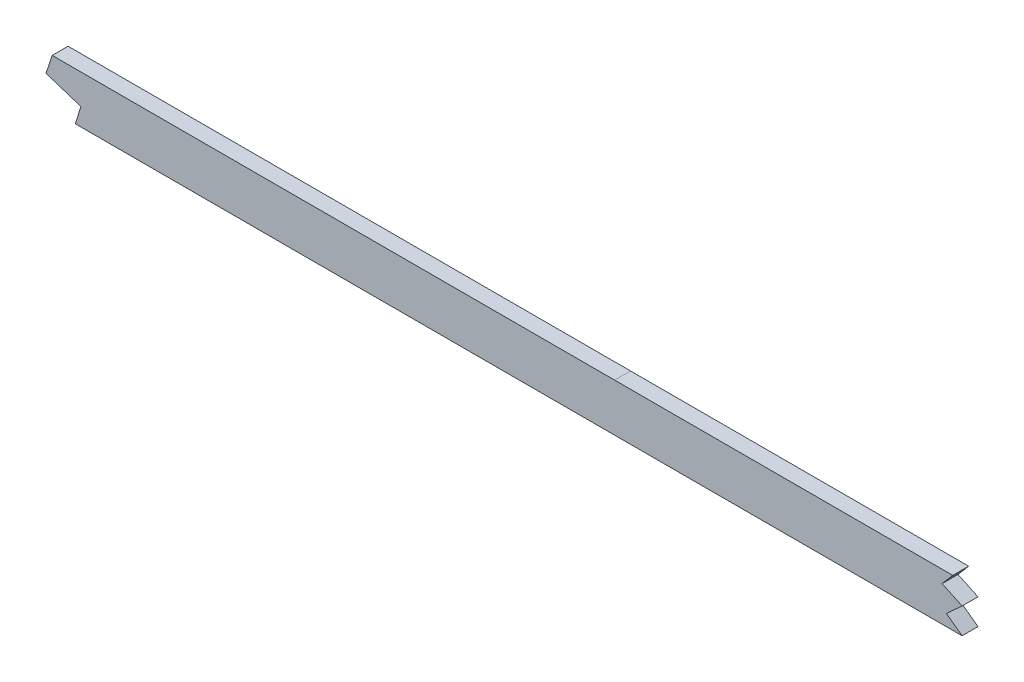
SolidWorks part; units mm, degrees
ref_plane "Front Plane" through (0, 0, 0) normal (0, 0, 1) x (1, 0, 0)
ref_plane "Top Plane" through (0, 0, 0) normal (0, 1, 0) x (1, 0, 0)
ref_plane "Right Plane" through (0, 0, 0) normal (1, 0, 0) x (0, 0, -1)
sketch "Sketch1" plane through (0, 0, 0) normal (0, 0, 1) x (1, 0, 0)
  line L0 (1046.2855, 53.4707) -> (499.61, 53.4707) construction
  line L1 (55, 0) -> (-55, 0) construction
  line L2 (1046.2855, -53.4707) -> (499.61, -53.4707)
  line L3 (1046.2855, -34.4207) -> (499.61, -34.4207)
  line L4 (99.06, -18.1493) -> (99.06, -37.7415)
  line L5 (2669.54, 9.5231) -> (2669.54, -9.569)
  spline S0 degree 5 poles (2699.7923, 7.5245) (2639.6368, 11.6572) (2579.4813, 15.4358) (2518.4981, 19.1485) (2436.3555, 23.2524) (2354.213, 26.6315) (2332.5703, 27.481) (2156.2686, 34.3778) (1979.9669, 41.6286) (1824.1143, 52.7713) (1636.9286, 53.5796) (1449.7429, 53.454) (1418.0067, 53.4707) (1324.8993, 53.4707) (1231.7919, 53.4707) (1170.4413, 53.4707) (1108.7841, 53.4707) (1047.1269, 53.4707) (1046.8464, 53.4707) (1046.5659, 53.4707) (1046.2855, 53.4707) knots 100.654805 100.654805 100.654805 100.654805 100.654805 100.654805 130.927897 130.927897 130.927897 141.337055 141.337055 141.337055 218.101815 218.101815 218.101815 233.772059 233.772059 233.772059 264.077723 264.077723 264.077723 264.216209 264.216209 264.216209 264.216209 264.216209 264.216209 weights 1 1 1 1 1 1 1 1 1 1 1 1 1 1 1 1 1 1 1 1 1 construction
  spline S1 degree 5 poles (499.61, 53.4707) (492.1368, 53.4707) (484.7543, 53.4707) (477.443, 53.4707) (448.5166, 53.4707) (419.5901, 53.4707) (398.3681, 53.4707) (355.6475, 53.4707) (312.927, 53.4707) (289.2351, 53.4703) (265.365, 53.4707) (241.4948, 53.4707) (241.4716, 53.4707) (241.4484, 53.4707) (241.4251, 53.4707) knots 19.90683 19.90683 19.90683 19.90683 19.90683 19.90683 23.637897 23.637897 23.637897 34.276546 34.276546 34.276546 46.401341 46.401341 46.401341 46.413154 46.413154 46.413154 46.413154 46.413154 46.413154 weights 1 1 1 1 1 1 1 1 1 1 1 1 1 1 1 construction
  spline S2 degree 5 poles (241.4251, 53.4707) (224.2869, 53.4707) (207.1495, 53.4673) (190.2039, 52.6866) (151.6561, 49.0319) (113.1083, 41.5037) (91.9499, 36.3426) (71.313, 30.9696) (50.6762, 24.7565) knots 0 0 0 0 0 0 8.713816 8.713816 8.713816 19.90683 19.90683 19.90683 19.90683 19.90683 19.90683 weights 1 1 1 1 1 1 1 1 1 construction
  spline S3 degree 5 poles (241.4251, -53.4707) (224.2869, -53.4707) (207.1495, -53.4673) (190.2039, -52.6866) (151.6561, -49.0319) (113.1083, -41.5037) (91.9499, -36.3426) (71.313, -30.9696) (50.6762, -24.7565) knots 0 0 0 0 0 0 8.713816 8.713816 8.713816 19.90683 19.90683 19.90683 19.90683 19.90683 19.90683 weights 1 1 1 1 1 1 1 1 1
  spline S4 degree 5 poles (499.61, -53.4707) (492.1368, -53.4707) (484.7543, -53.4707) (477.443, -53.4707) (448.5166, -53.4707) (419.5901, -53.4707) (398.3681, -53.4707) (355.6475, -53.4707) (312.927, -53.4707) (289.2351, -53.4703) (265.365, -53.4707) (241.4948, -53.4707) (241.4716, -53.4707) (241.4484, -53.4707) (241.4251, -53.4707) knots 19.90683 19.90683 19.90683 19.90683 19.90683 19.90683 23.637897 23.637897 23.637897 34.276546 34.276546 34.276546 46.401341 46.401341 46.401341 46.413154 46.413154 46.413154 46.413154 46.413154 46.413154 weights 1 1 1 1 1 1 1 1 1 1 1 1 1 1 1
  spline S5 degree 5 poles (2699.7923, -7.5245) (2639.6368, -11.6572) (2579.4813, -15.4358) (2518.4981, -19.1485) (2436.3555, -23.2524) (2354.213, -26.6315) (2332.5703, -27.481) (2156.2686, -34.3778) (1979.9669, -41.6286) (1824.1143, -52.7713) (1636.9286, -53.5796) (1449.7429, -53.454) (1418.0067, -53.4707) (1324.8993, -53.4707) (1231.7919, -53.4707) (1170.4413, -53.4707) (1108.7841, -53.4707) (1047.1269, -53.4707) (1046.8464, -53.4707) (1046.5659, -53.4707) (1046.2855, -53.4707) knots 100.654805 100.654805 100.654805 100.654805 100.654805 100.654805 130.927897 130.927897 130.927897 141.337055 141.337055 141.337055 218.101815 218.101815 218.101815 233.772059 233.772059 233.772059 264.077723 264.077723 264.077723 264.216209 264.216209 264.216209 264.216209 264.216209 264.216209 weights 1 1 1 1 1 1 1 1 1 1 1 1 1 1 1 1 1 1 1 1 1
  spline S6 degree 1 poles (2698.4867, 11.4807) (1046.2855, -34.4207) knots 0 0 1 1 construction
  spline S7 degree 1 poles (499.61, -34.4207) (241.4252, -34.4207) knots 0 0 1 1 construction
  spline S8 degree 1 poles (241.4252, -34.4207) (56.168, -6.5153) knots 0 0 1 1 construction
  spline S9 degree 3 poles (2698.4867, 11.4807) (2691.2474, 10.9833) (2679.1952, 10.1655) (2662.2765, 9.0388) (2635.6663, 7.2925) (2596.8577, 4.8261) (2545.7297, 1.7583) (2494.4053, -1.0986) (2451.533, -3.2666) (2417.1983, -4.8671) (2391.4571, -6.0036) (2365.6347, -7.0869) (2339.5463, -8.1377) (2313.4661, -9.1651) (2287.6124, -10.1795) (2261.7633, -11.201) (2227.2853, -12.5838) (2184.1756, -14.3661) (2132.4291, -16.6074) (2063.4255, -19.7089) (1977.1749, -23.7005) (1873.7325, -28.1494) (1770.3746, -31.6575) (1667.0857, -33.7931) (1581.0111, -34.3832) (1512.074, -34.4278) (1443.0615, -34.4095) (1356.8009, -34.4244) (1218.7946, -34.4185) (1115.289, -34.4207) (1046.2855, -34.4207) knots 100.654805 100.654805 100.654805 100.654805 102.842388 104.300777 105.766098 110.877392 115.988686 121.09998 126.211274 128.766921 131.322568 133.878215 136.433862 138.989509 141.545156 144.100803 146.656449 151.767743 156.879037 161.990331 172.212919 182.435507 192.658094 202.880682 213.10327 218.214564 223.325858 233.548445 243.771033 264.216209 264.216209 264.216209 264.216209
  spline S10 degree 3 poles (499.61, -34.4207) (488.6147, -34.4207) (472.2364, -34.4207) (449.9402, -34.4207) (427.7713, -34.4207) (405.8747, -34.4207) (384.5849, -34.4207) (368.9002, -34.4207) (353.3766, -34.4207) (332.6085, -34.4207) (306.2878, -34.4206) (274.0235, -34.4205) (252.271, -34.4207) (241.4252, -34.4207) knots 19.90683 19.90683 19.90683 19.90683 23.22012 24.876765 26.533411 29.846701 31.503346 33.159992 34.816637 36.473282 39.786573 43.099863 46.413154 46.413154 46.413154 46.413154
  spline S11 degree 3 poles (241.4252, -34.4207) (239.3949, -34.4207) (235.3223, -34.4205) (227.2744, -34.3987) (217.3194, -34.2975) (205.5307, -33.9764) (189.9633, -33.2126) (170.697, -31.5435) (147.5333, -28.3144) (125.4828, -24.2021) (107.4399, -20.1965) (92.2061, -16.4882) (75.9505, -12.2555) (63.6202, -8.7589) (56.168, -6.5153) knots 0 0 0 0 0.622088 1.244177 2.488354 3.732531 4.976707 7.465061 9.953415 12.441768 14.558235 15.802412 17.418476 19.90683 19.90683 19.90683 19.90683
  point P2 (0, 0)
  dimension "D1" = 50.6762
  dimension "D3" = 99.06
  dimension "D4" = 2669.54
  dimension "D2" = 19.05
extrude "Boss-Extrude1" add sketch "Sketch1" along normal mid plane 6.35 contours S10 S11 L4 S3 S4 L2 S5 L5 S9 L3
sketch "Sketch2" plane through (0, 0, 3.175) normal (0, 0, 1) x (1, 0, 0)
  line L0 (2187.01, -14.2633) -> (2312.9875, -14.2633)
  line L1 (2312.9875, -14.2633) -> (2312.9875, -9.1833)
  spline S0 degree 3 poles (689.0175, 232.3189) (4033.8285, 148.9311) (3356.6623, 54.6077) (2635.6663, 7.2925) (2596.8577, 4.8261) (2545.7297, 1.7583) (2494.4053, -1.0986) (2451.533, -3.2666) (2417.1983, -4.8671) (2391.4571, -6.0036) (2365.6347, -7.0869) (2339.5463, -8.1377) (2313.4661, -9.1651) (2287.6124, -10.1795) (2261.7633, -11.201) (2227.2853, -12.5838) (2184.1756, -14.3661) (2132.4291, -16.6074) (2063.4255, -19.7089) (1977.1749, -23.7005) (1873.7325, -28.1494) (1770.3746, -31.6575) (1667.0857, -33.7931) (1581.0111, -34.3832) (1512.074, -34.4278) (1443.0615, -34.4095) (1356.8009, -34.4244) (551.9641, -34.3896) (-218.4198, -34.7282) (-953.6342, -29.9632) knots -106.828462 -106.828462 -106.828462 -106.828462 104.300777 105.766098 110.877392 115.988686 121.09998 126.211274 128.766921 131.322568 133.878215 136.433862 138.989509 141.545156 144.100803 146.656449 151.767743 156.879037 161.990331 172.212919 182.435507 192.658094 202.880682 213.10327 218.214564 223.325858 233.548445 243.771033 461.793666 461.793666 461.793666 461.793666 only from (2669.54, 9.5231) to (1046.2855, -34.4207) construction
  spline S1 degree 3 poles (2669.54, 9.5231) (2667.1265, 9.3624) (2659.8616, 8.8803) (2635.6663, 7.2925) (2596.8577, 4.8261) (2545.7297, 1.7583) (2494.4053, -1.0986) (2451.533, -3.2666) (2417.1983, -4.8671) (2391.4571, -6.0036) (2365.6347, -7.0869) (2339.5463, -8.1377) (2313.4661, -9.1651) (2287.6124, -10.1795) (2261.7633, -11.201) (2227.2853, -12.5838) (2184.1756, -14.3661) (2132.4291, -16.6074) (2063.4255, -19.7089) (1977.1749, -23.7005) (1873.7325, -28.1494) (1770.3746, -31.6575) (1667.0857, -33.7931) (1581.0111, -34.3832) (1512.074, -34.4278) (1443.0615, -34.4095) (1356.8009, -34.4244) (1218.7946, -34.4185) (1115.289, -34.4207) (1046.2855, -34.4207) knots 103.571583 103.571583 103.571583 103.571583 104.300777 105.766098 110.877392 115.988686 121.09998 126.211274 128.766921 131.322568 133.878215 136.433862 138.989509 141.545156 144.100803 146.656449 151.767743 156.879037 161.990331 172.212919 182.435507 192.658094 202.880682 213.10327 218.214564 223.325858 233.548445 243.771033 264.216209 264.216209 264.216209 264.216209
  point P2 (0, 0)
  spline M9 degree 3 poles (2698.4867, 11.4807) (2691.2474, 10.9833) (2679.1952, 10.1655) (2662.2765, 9.0388) (2635.6663, 7.2925) (2596.8577, 4.8261) (2545.7297, 1.7583) (2494.4053, -1.0986) (2451.533, -3.2666) (2417.1983, -4.8671) (2391.4571, -6.0036) (2365.6347, -7.0869) (2339.5463, -8.1377) (2313.4661, -9.1651) (2287.6124, -10.1795) (2261.7633, -11.201) (2227.2853, -12.5838) (2184.1756, -14.3661) (2132.4291, -16.6074) (2063.4255, -19.7089) (1977.1749, -23.7005) (1873.7325, -28.1494) (1770.3746, -31.6575) (1667.0857, -33.7931) (1581.0111, -34.3832) (1512.074, -34.4278) (1443.0615, -34.4095) (1356.8009, -34.4244) (1218.7946, -34.4185) (1115.289, -34.4207) (1046.2855, -34.4207) knots 100.654805 100.654805 100.654805 100.654805 102.842388 104.300777 105.766098 110.877392 115.988686 121.09998 126.211274 128.766921 131.322568 133.878215 136.433862 138.989509 141.545156 144.100803 146.656449 151.767743 156.879037 161.990331 172.212919 182.435507 192.658094 202.880682 213.10327 218.214564 223.325858 233.548445 243.771033 264.216209 264.216209 264.216209 264.216209 only from (2669.54, 9.5231) to (1046.2855, -34.4207)
  dimension "D1" = 2312.9875
  dimension "D2" = 5.08
extrude "Cut-Extrude1" cut sketch "Sketch2" against normal through all contours L0 L1 M9
fillet "Fillet1" radius 2.54 6 edges at (2669.54, -9.569, 0) (2669.54, 9.5231, 0) (99.06, -37.7415, 0) (99.06, -18.1493, 0) (2312.9875, -14.2633, 0)
sketch "Sketch3" plane through (0, 0, 3.175) normal (0, 0, 1) x (1, 0, 0)
  line L3 (1046.2855, -34.4207) -> (499.61, -34.4207) construction
  line L4 (1046.2855, -53.4707) -> (499.61, -53.4707) construction
  line L12 (821.5189, -34.4207) -> (819.0473, -41.8744)
  line L13 (819.0473, -41.8744) -> (833.0048, -46.3842)
  line L14 (833.0048, -46.3842) -> (830.7563, -53.4707)
  line L15 (1181.434, -34.42) -> (1177.1364, -39.4111)
  line L16 (1177.1364, -39.4111) -> (1185.136, -43.1614)
  line L17 (1185.136, -43.1614) -> (1178.8578, -48.8791)
  line L18 (1178.8578, -48.8791) -> (1185.136, -53.4707)
  line L28 (821.5189, -34.4207) -> (821.5189, 94.2667)
  line L29 (821.5189, 94.2667) -> (65.8226, 75.5237)
  line L30 (65.8226, 75.5237) -> (71.3333, -146.6591)
  line L31 (71.3333, -146.6591) -> (833.0048, -88.3772)
  line L32 (833.0048, -88.3772) -> (830.7563, -53.4707)
  line L33 (1181.434, -34.42) -> (1181.434, 94.2667)
  line L34 (1181.434, 94.2667) -> (2840.4603, 201.132)
  line L35 (2840.4603, 201.132) -> (2840.4603, -301.932)
  line L36 (2840.4603, -301.932) -> (1178.8578, -73.8328)
  line L37 (1178.8578, -73.8328) -> (1185.136, -53.4707)
  spline S2 degree 3 poles (2187.01, -14.2633) (2186.0643, -14.3032) (2167.8725, -15.0722) (2132.4291, -16.6074) (2063.4255, -19.7089) (1977.1749, -23.7005) (1873.7325, -28.1494) (1770.3746, -31.6575) (1667.0857, -33.7931) (1581.0111, -34.3832) (1512.074, -34.4278) (1443.0615, -34.4095) (1356.8009, -34.4244) (1218.7946, -34.4185) (1115.289, -34.4207) (1046.2855, -34.4207) knots 151.487489 151.487489 151.487489 151.487489 151.767743 156.879037 161.990331 172.212919 182.435507 192.658094 202.880682 213.10327 218.214564 223.325858 233.548445 243.771033 264.216209 264.216209 264.216209 264.216209 construction
  spline S3 degree 5 poles (2667.1682, -9.7266) (2613.4902, -13.2886) (2559.6385, -16.6207) (2505.242, -19.8061) (2429.7275, -23.525) (2354.213, -26.6315) (2332.5703, -27.481) (2156.2686, -34.3778) (1979.9669, -41.6286) (1824.1143, -52.7713) (1636.9286, -53.5796) (1449.7429, -53.454) (1418.0067, -53.4707) (1324.8993, -53.4707) (1231.7919, -53.4707) (1170.4413, -53.4707) (1108.7841, -53.4707) (1047.1269, -53.4707) (1046.8464, -53.4707) (1046.5659, -53.4707) (1046.2855, -53.4707) knots 103.937447 103.937447 103.937447 103.937447 103.937447 103.937447 130.927897 130.927897 130.927897 141.337055 141.337055 141.337055 218.101815 218.101815 218.101815 233.772059 233.772059 233.772059 264.077723 264.077723 264.077723 264.216209 264.216209 264.216209 264.216209 264.216209 264.216209 weights 1 1 1 1 1 1 1 1 1 1 1 1 1 1 1 1 1 1 1 1 1 construction
extrude "Cut-Extrude2" cut sketch "Sketch3" against normal blind 7.62
